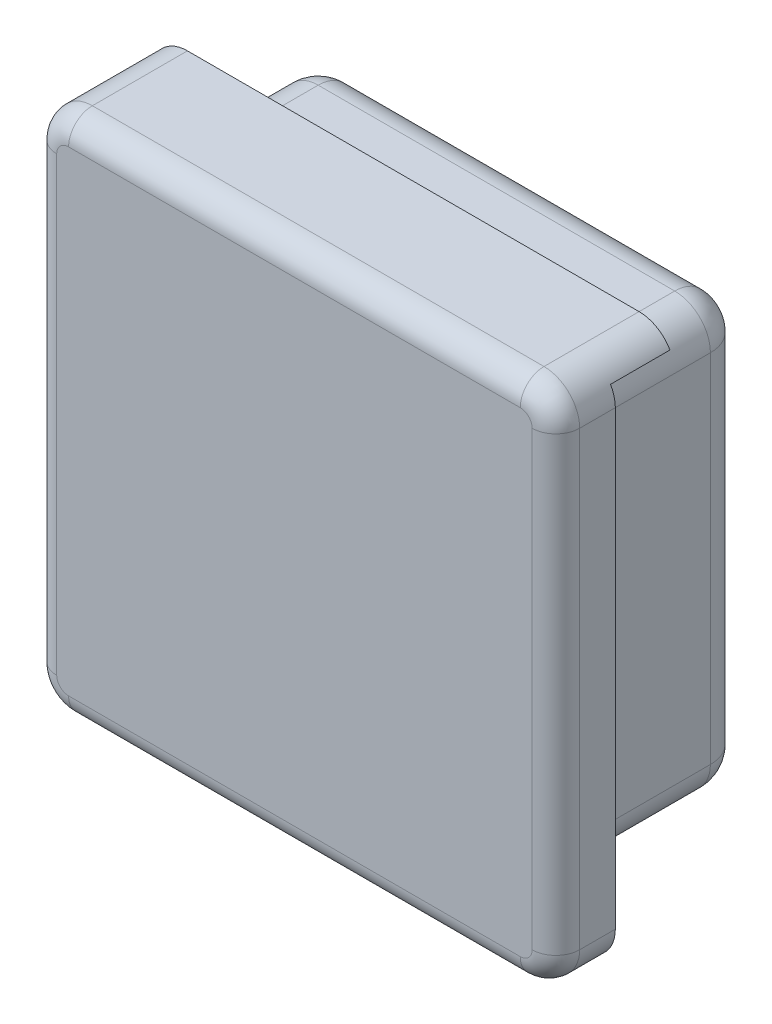
SolidWorks part; units mm, degrees
ref_plane "Plan de face" through (0, 0, 0) normal (0, 0, 1) x (1, 0, 0)
ref_plane "Plan de dessus" through (0, 0, 0) normal (0, 1, 0) x (1, 0, 0)
ref_plane "Plan de droite" through (0, 0, 0) normal (1, 0, 0) x (0, 0, -1)
sketch "Esquisse2" plane through (0, 0, 0) normal (0, 0, 1) x (1, 0, 0)
  line L1 (0, 0) -> (44, 0)
  line L2 (0, 0) -> (0, 44)
  line L3 (0, 44) -> (44, 44)
  line L4 (44, 0) -> (44, 44)
  dimension "D1" = 44
extrude "Boss.-Extru.1" add sketch "Esquisse2" along normal blind 10
sketch "Esquisse3" plane through (0, 0, 0) normal (0, 0, -1) x (-1, 0, 0)
  line L0 (-44, 44) -> (0, 44) construction
  line L1 (-40, 4) -> (-4, 4)
  line L2 (-40, 4) -> (-40, 40)
  line L3 (-40, 40) -> (-4, 40)
  line L4 (-4, 4) -> (-4, 40)
  line L5 (0, 44) -> (0, 0) construction
  dimension "D1" = 36
  dimension "D2" = 36
  dimension "D3" = 4
  dimension "D4" = 4
extrude "Boss.-Extru.2" add sketch "Esquisse3" along normal blind 10
sketch "Esquisse4" plane through (0, 0, 0) normal (0, 0, -1) x (-1, 0, 0)
  line L0 (-40, 40) -> (-4, 40)
  line L1 (-4, 40) -> (-4, 4)
  line L2 (-4, 4) -> (-40, 4)
  line L3 (-40, 4) -> (-40, 40)
  line L4 (-44, 42.5) -> (-1.5, 42.5)
  line L5 (-44, 0) -> (-44, 44) construction
  line L6 (-1.5, 42.5) -> (-1.5, 0)
  line L7 (0, 0) -> (-44, 0) construction
  line L8 (-1.5, 0) -> (-44, 0)
  line L9 (-44, 0) -> (-44, 42.5)
  line L10 (-44, 44) -> (0, 44) construction
  dimension "D1" = 1.5
  dimension "D2" = 2.5
extrude "Enlèv. mat.-Extru.1" cut sketch "Esquisse4" against normal blind 5
fillet "Congé1" radius 3 13 edges at (22, 40, -10) (4, 22, -10) (22, 4, -10) (40, 22, -10) (44, 0, 7.5) (44, 44, 5) (0, 0, 5) (0, 44, 5) (1.5, 42.5, 2.5) (4, 4, -2.5) (4, 40, -2.5) (40, 4, -2.5) (40, 40, -2.5)
fillet "Congé2" radius 2 8 edges at (0.8787, 0.8787, 10) (0, 22, 10) (0.8787, 43.1213, 10) (22, 44, 10) (43.1213, 43.1213, 10) (44, 22, 10) (43.1213, 0.8787, 10) (22, 0, 10)
